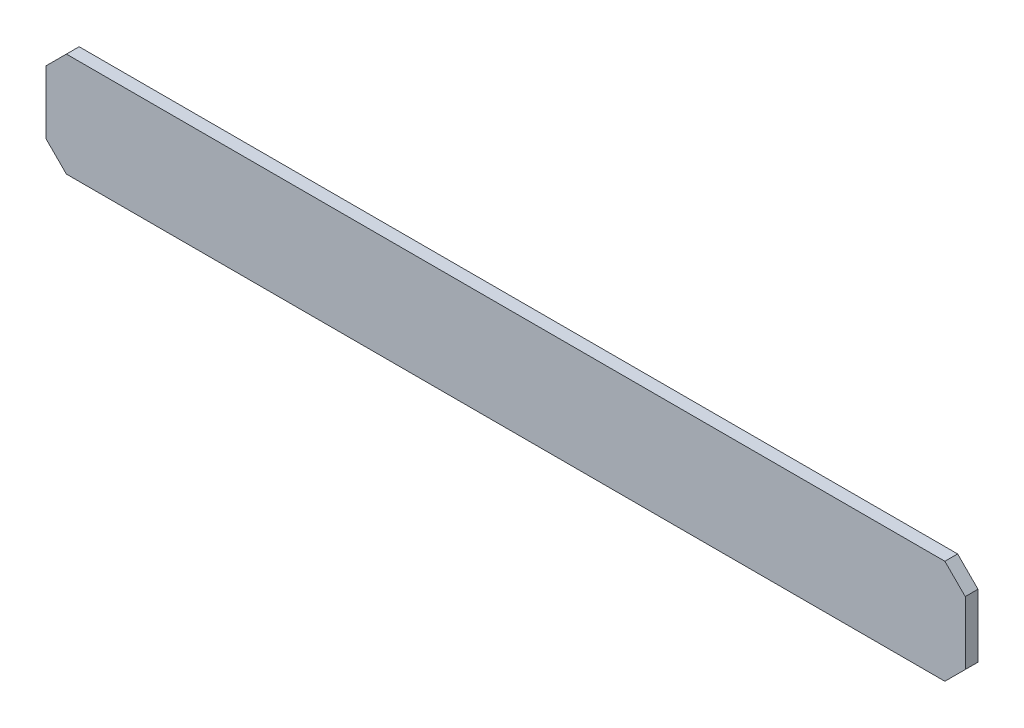
SolidWorks part; units mm, degrees
material "ABS PC"
ref_plane "Front Plane" through (0, 0, 0) normal (0, 0, 1) x (1, 0, 0)
ref_plane "Top Plane" through (0, 0, 0) normal (0, 1, 0) x (1, 0, 0)
ref_plane "Right Plane" through (0, 0, 0) normal (1, 0, 0) x (0, 0, -1)
sketch "Sketch2" plane through (0, 0, -4.7327) normal (0, 0, 1) x (1, 0, 0)
  line L0 (-56.769, -63.0969) -> (-44.831, -63.0969) construction
  line L1 (57.277, -50.1429) -> (-57.277, -50.1429)
  line L2 (57.277, -50.1429) -> (57.277, -63.0969)
  line L3 (57.277, -63.0969) -> (-57.277, -63.0969)
  line L4 (-57.277, -50.1429) -> (-57.277, -63.0969)
  line L5 (57.277, -50.1429) -> (-57.277, -63.0969) construction
  line L6 (57.277, -63.0969) -> (-57.277, -50.1429) construction
  line L7 (-57.277, -50.6509) -> (-57.277, -62.5889) construction
  point P0 (0, -56.6199)
extrude "Boss-Extrude1" add sketch "Sketch2" along normal blind 1.5875
chamfer "Chamfer1" distance 2.54 angle 45 4 edges at (-57.277, -50.1429, -3.9389) (-57.277, -63.0969, -3.9389) (57.277, -50.1429, -3.9389) (57.277, -63.0969, -3.9389)
